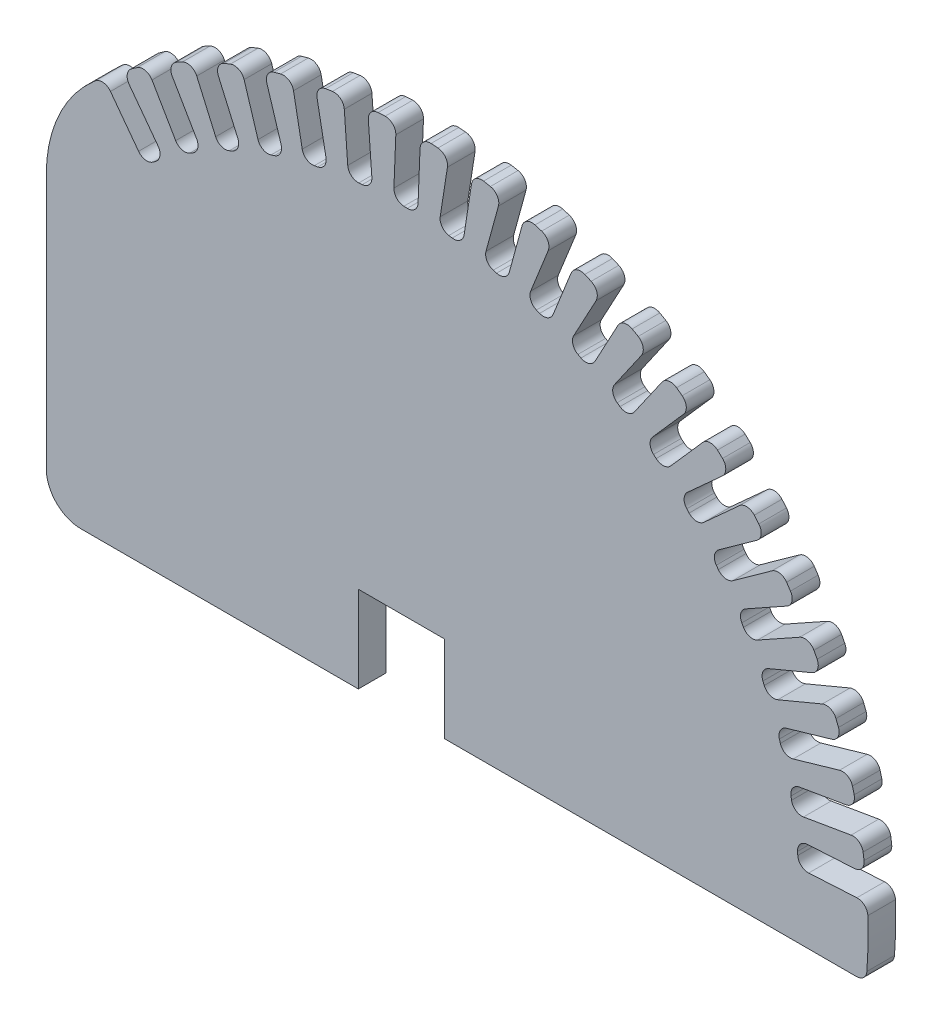
SolidWorks part; units mm, degrees
ref_plane "Plan de face" through (0, 0, 0) normal (0, 0, 1) x (1, 0, 0)
ref_plane "Plan de dessus" through (0, 0, 0) normal (0, 1, 0) x (1, 0, 0)
ref_plane "Plan de droite" through (0, 0, 0) normal (1, 0, 0) x (0, 0, -1)
sketch "Esquisse1" plane through (0, 0, 0) normal (0, 0, 1) x (1, 0, 0)
  line L2 (0, 0) -> (0, 12.5) construction
  line L3 (0, 12.5) -> (12.5, 12.5)
  line L4 (12.5, 12.5) -> (12.5, 0)
  line L5 (0, 12.5) -> (-12.5, 12.5)
  line L6 (-12.5, 12.5) -> (-12.5, 0)
  line L7 (-134.4201, -12.5) -> (134.4201, -12.5)
  line L9 (12.5, 0) -> (12.5, -12.5)
  line L10 (-12.5, 0) -> (-12.5, -12.5)
  arc A0 (-134.4201, -12.5) -> (134.4201, -12.5) centre (0, 0) cw
  dimension "D2" = 135
  dimension "D1" = 12.5
  dimension "D3" = 25
extrude "Boss.-Extru.1" add sketch "Esquisse1" along normal blind 8
sketch "Esquisse2" plane through (0, 0, 8) normal (0, 0, 1) x (1, 0, 0)
  line L0 (-102.8044, -12.5) -> (-102.8044, 87.5)
  line L2 (-102.8044, 87.5) -> (-135, 87.5)
  line L3 (-135, 87.5) -> (-135, -12.5)
  line L4 (-134.4201, -12.5) -> (-12.5, -12.5) construction
  line L5 (-102.8044, -12.5) -> (-135, -12.5)
  arc A0 (134.4201, -12.5) -> (-134.4201, -12.5) centre (0, 0) ccw construction
  dimension "D1" = 100
  dimension "D2" = 32.1956
extrude "Enlèv. mat.-Extru.1" cut sketch "Esquisse2" against normal through all
sketch "Esquisse3" plane through (0, 0, 8) normal (0, 0, 1) x (1, 0, 0)
  line L0 (0, 0) -> (-80.6354, 108.2725) construction
  line L1 (-80.6354, 108.2725) -> (-68.6894, 92.2321)
  line L2 (-68.6894, 92.2321) -> (-74.3035, 88.051)
  line L3 (-74.3035, 88.051) -> (-86.141, 103.9458)
  arc A0 (134.4201, -12.5) -> (-102.8044, 87.5) centre (0, 0) ccw construction
  arc A1 (-86.141, 103.9458) -> (-80.6354, 108.2725) centre (0, 0) cw
  dimension "D1" = 7
  dimension "D2" = 20
extrude "Enlèv. mat.-Extru.2" cut sketch "Esquisse3" against normal through all
fillet "Congé1" radius 3 4 edges at (-68.6894, 92.2321, 4) (-80.6354, 108.2725, 4) (-86.141, 103.9458, 4) (-74.3035, 88.051, 4)
pattern_circular "Répétition circulaire1" count 20 every 6.5 about axis through (0, 0, 0) along (0, 0, 1) of "Enlèv. mat.-Extru.2", "Congé1"
fillet "Congé2" radius 40 1 edges at (-102.8044, 87.5, 4)
fillet "Congé3" radius 10 1 edges at (-102.8044, -12.5, 4)
fillet "Congé5" radius 3 1 edges at (134.4201, -12.5, 4)
